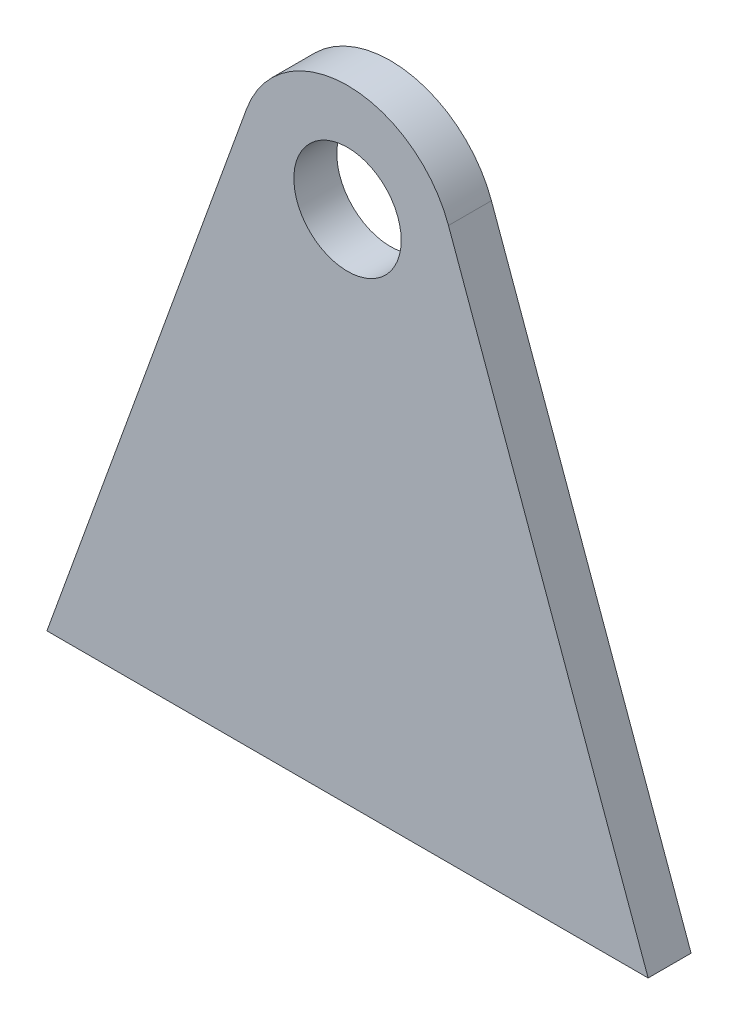
SolidWorks part; units mm, degrees
ref_plane "Front Plane" through (0, 0, 0) normal (0, 0, 1) x (1, 0, 0)
ref_plane "Top Plane" through (0, 0, 0) normal (0, 1, 0) x (1, 0, 0)
ref_plane "Right Plane" through (0, 0, 0) normal (1, 0, 0) x (0, 0, -1)
sketch "Sketch1" plane through (0, 0, 0) normal (0, 0, 1) x (1, 0, 0)
  line L0 (-203.9215, 0) -> (172.4324, 0) construction
  line L1 (0, 402.0313) -> (0, -105.456) construction
  line L2 (-140, 0) -> (140, 0)
  line L3 (140, 0) -> (47.0176, 257.0102)
  line L4 (-140, 0) -> (-47.0176, 257.0102)
  arc A0 (-47.0176, 257.0102) -> (47.0176, 257.0102) centre (0, 240) cw
  circle A1 centre (0, 240) radius 25
  point P10 (0, 402.0313)
  point P11 (0, 0)
  point P13 (0, 0)
  point P14 (-101.7728, 0)
  point P15 (0, 0)
  point P16 (-141.5589, 0)
  point P17 (-203.9215, 0)
  dimension "D1" = 50
  dimension "D2" = 50
  dimension "D3" = 240
  dimension "D4" = 280
extrude "Boss-Extrude1" add sketch "Sketch1" against normal blind 20
